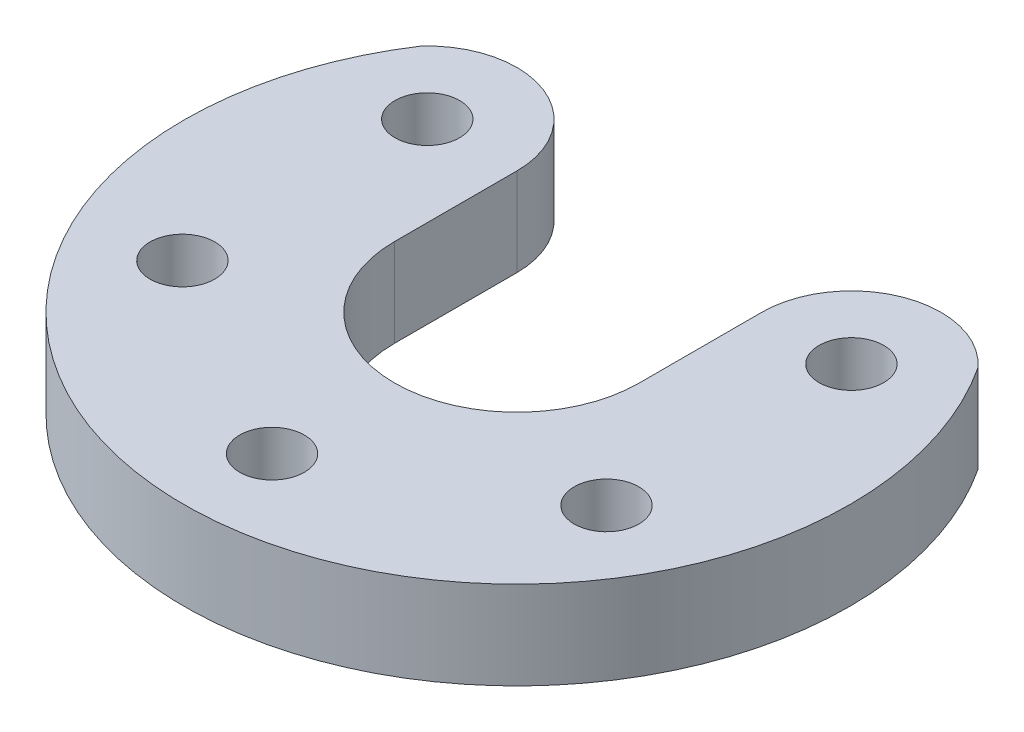
SolidWorks part; units mm, degrees
ref_plane "Front Plane" through (0, 0, 0) normal (0, 0, 1) x (1, 0, 0)
ref_plane "Top Plane" through (0, 0, 0) normal (0, 1, 0) x (1, 0, 0)
ref_plane "Right Plane" through (0, 0, 0) normal (1, 0, 0) x (0, 0, -1)
sketch "Sketch1" plane through (0, 0, 0) normal (0, 1, 0) x (1, 0, 0)
  line L0 (6.25, 0) -> (6.25, 6.25)
  line L2 (-6.25, 6.25) -> (-6.25, 0)
  arc A0 (-6.25, 0) -> (6.25, 0) centre (0, 0) ccw
  arc A1 (-14.2169, 9.321) -> (14.2169, 9.321) centre (0, 0) ccw
  arc A2 (-6.25, 6.25) -> (-15.1806, 7.6517) centre (-10.8253, 6.25) ccw
  circle A3 centre (10.8253, 6.25) radius 1.65
  circle A4 centre (10.8253, -6.25) radius 1.65
  circle A5 centre (0, -12.5) radius 1.65
  circle A6 centre (-10.8253, -6.25) radius 1.65
  circle A7 centre (-10.8253, 6.25) radius 1.65
  arc A8 (15.1806, 7.6517) -> (6.25, 6.25) centre (10.8253, 6.25) ccw
  point P21 (0, 0)
  dimension "D1" = 12.5
  dimension "D2" = 34
extrude "Boss-Extrude1" add sketch "Sketch1" along normal blind 4.5 contours A1 A8 L0 A0 L2 A2 A3 A4 A5 A6 A7
